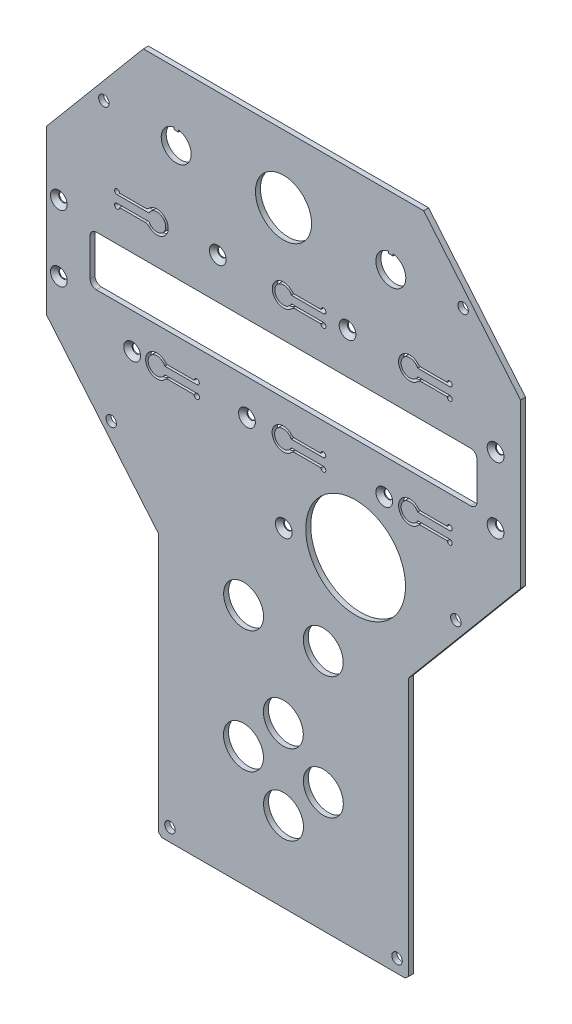
SolidWorks part; units mm, degrees
ref_plane "Plano frontal" through (0, 0, 0) normal (0, 0, 1) x (1, 0, 0)
ref_plane "Plano superior" through (0, 0, 0) normal (0, 1, 0) x (1, 0, 0)
ref_plane "Plano direito" through (0, 0, 0) normal (1, 0, 0) x (0, 0, -1)
sketch "Esboço1" plane through (0, 0, 0) normal (0, 0, 1) x (1, 0, 0)
  line L6 (55.321, 133.8096) -> (-57.007, 133.8096)
  line L7 (-57.007, 133.8096) -> (-95.843, 87.5267)
  line L8 (-95.843, 87.5267) -> (-95.843, 22.1402)
  line L9 (-95.843, 22.1402) -> (-50.843, -31.4887)
  line L10 (-50.843, -31.4887) -> (-50.843, -135.0827)
  line L11 (-50.843, -135.0827) -> (-49.5229, -136.1904)
  line L12 (-49.5229, -136.1904) -> (47.8369, -136.1904)
  line L13 (49.157, -135.0827) -> (47.8369, -136.1904)
  line L14 (49.157, -31.4887) -> (49.157, -135.0827)
  line L15 (94.157, 22.1402) -> (49.157, -31.4887)
  line L16 (94.157, 87.5267) -> (94.157, 22.1402)
  line L17 (55.321, 133.8096) -> (94.157, 87.5267)
  point P16 (-0.843, -136.1904)
  point P17 (-0.843, 133.8096)
extrude "Ressalto-extrusão1" add sketch "Esboço1" along normal blind 2
sketch "Esboço2" plane through (0, 0, 2) normal (0, 0, 1) x (1, 0, 0)
  line L0 (-0.843, -146.6722) -> (-0.843, 180.0647) construction
  line L1 (-95.843, 87.5267) -> (-95.843, 22.1402) construction
  line L2 (55.321, 133.8096) -> (-57.007, 133.8096) construction
  line L3 (-95.843, 22.1402) -> (-50.843, -31.4887) construction
  line L6 (49.157, -135.0827) -> (49.157, -31.4887) construction
  line L7 (-49.5229, -136.1904) -> (47.8369, -136.1904) construction
  line L9 (-50.843, -31.4887) -> (-50.843, -135.0827) construction
  circle A0 centre (-72.8144, 107.9499) radius 2.1
  circle A1 centre (-46.343, -130.9644) radius 2.1
  circle A2 centre (44.657, -130.9644) radius 2.1
  circle A3 centre (71.1284, 107.9499) radius 2.1
  circle A4 centre (-69.8958, -1.7817) radius 2.1
  circle A5 centre (68.2098, -1.7817) radius 2.1
  dimension "D1" = 23.0286
  dimension "D2" = 4.5
  dimension "D3" = 4.5
  dimension "D7" = 25.8597
  dimension "D4" = 5.226
  dimension "D11" = 4.5
extrude "Corte-extrusão1" cut sketch "Esboço2" against normal up to next
sketch "Esboço3" plane through (0, 0, 2) normal (0, 0, 1) x (1, 0, 0)
  line L0 (-95.843, 87.5267) -> (-95.843, 22.1402) construction
  line L1 (-49.5229, -136.1904) -> (47.8369, -136.1904) construction
  line L2 (-75.843, 40.8096) -> (74.157, 40.8096)
  line L3 (-78.343, 43.3096) -> (-78.343, 58.3096)
  line L4 (-75.843, 60.8096) -> (74.157, 60.8096)
  line L5 (76.657, 43.3096) -> (76.657, 58.3096)
  line L6 (-78.343, 40.8096) -> (76.657, 60.8096) construction
  line L7 (-78.343, 60.8096) -> (76.657, 40.8096) construction
  arc A0 (74.157, 60.8096) -> (76.657, 58.3096) centre (74.157, 58.3096) cw
  arc A1 (74.157, 40.8096) -> (76.657, 43.3096) centre (74.157, 43.3096) ccw
  arc A2 (-75.843, 40.8096) -> (-78.343, 43.3096) centre (-75.843, 43.3096) cw
  arc A3 (-78.343, 58.3096) -> (-75.843, 60.8096) centre (-75.843, 58.3096) cw
  dimension "D1" = 2.5
  dimension "D2" = 155
  dimension "D3" = 20
  dimension "D4" = 17.5
  dimension "D5" = 177
extrude "Corte-extrusão2" cut sketch "Esboço3" against normal up to next
sketch "Esboço4" plane through (0, 0, 2) normal (0, 0, 1) x (1, 0, 0)
  line L2 (-49.5229, -136.1904) -> (47.8369, -136.1904) construction
  line L3 (94.157, 22.1402) -> (94.157, 87.5267) construction
  circle A0 centre (28.0563, -0.1904) radius 20
  dimension "D1" = 136
  dimension "D2" = 66.1007
extrude "Corte-extrusão3" cut sketch "Esboço4" against normal up to next
sketch "Esboço5" plane through (0, 0, 2) normal (0, 0, 1) x (1, 0, 0)
  line L2 (55.321, 133.8096) -> (-57.007, 133.8096) construction
  line L3 (-44.743, 112.7417) -> (-44.743, 111.9417)
  line L4 (-44.743, 111.9417) -> (-42.943, 111.9417)
  line L5 (-42.943, 111.9417) -> (-42.943, 112.7417)
  line L6 (41.257, 112.7417) -> (41.257, 111.9417)
  line L7 (41.257, 111.9417) -> (43.057, 111.9417)
  line L8 (43.057, 111.9417) -> (43.057, 112.7417)
  circle A0 centre (-16.8949, -88.1059) radius 8
  circle A1 centre (15.1229, -88.1059) radius 8
  circle A2 centre (-0.843, -104.1412) radius 8
  circle A3 centre (-0.9097, -72.1234) radius 8
  circle A4 centre (-16.8357, -39.1393) radius 8
  circle A5 centre (15.0819, -39.1108) radius 8
  circle A6 centre (-0.843, 106.8096) radius 11.25
  arc A7 (-44.743, 112.7417) -> (-42.943, 112.7417) centre (-43.843, 106.8096) ccw
  arc A8 (41.257, 112.7417) -> (43.057, 112.7417) centre (42.157, 106.8096) ccw
  dimension "D11" = 27
  dimension "D12" = 43
  dimension "D13" = 43
  dimension "D14" = 22.5
  dimension "D15" = 12
  dimension "D16" = 12
  dimension "D18" = 1.8
  dimension "D19" = 0.9
  dimension "D20" = 0.8
  dimension "D21" = 1.8
  dimension "D22" = 0.9
  dimension "D23" = 0.8
extrude "Corte-extrusão4" cut sketch "Esboço5" against normal up to next
sketch "Esboço10" plane through (0, 0, 2) normal (0, 0, 1) x (1, 0, 0)
  line L3 (94.157, 22.1402) -> (94.157, 87.5267) construction
  line L4 (74.157, 60.8096) -> (-75.843, 60.8096) construction
  circle A0 centre (-61.4827, 26.6206) radius 1.75
  circle A1 centre (-15.4827, 26.6206) radius 1.75
  circle A2 centre (39.5173, 26.6206) radius 1.75
  circle A3 centre (84.131, 37.971) radius 1.6
  circle A4 centre (84.131, 64.471) radius 1.6
  circle A5 centre (-90.869, 64.471) radius 1.6
  circle A6 centre (-90.869, 37.971) radius 1.6
  circle A7 centre (-27.183, 77.1996) radius 1.75
  circle A8 centre (24.817, 77.1996) radius 1.75
  circle A9 centre (-0.7327, -4.3294) radius 2
  dimension "D1" = 69.3401
  dimension "D2" = 16.39
  dimension "D3" = 52
  dimension "D4" = 30.95
  dimension "D5" = 14.75
hole_wizard "Escareado para parafuso Allen sextavado escareado de M32" positions "3DSketch3" profile "Esboço11" countersink size "M3" standard "ISO" end condition through all
sketch3d "3DSketch3"
  point P0 (-90.869, 64.471, 2)
  point P3 (-90.869, 37.971, 2)
  point P6 (-61.4827, 26.6206, 2)
  point P9 (-15.4827, 26.6206, 2)
  point P12 (39.5173, 26.6206, 2)
  point P15 (84.131, 37.971, 2)
  point P18 (84.131, 64.471, 2)
  point P21 (24.817, 77.1996, 2)
  point P24 (-27.183, 77.1996, 2)
  point P32 (-0.7327, -4.3294, 2)
sketch "Esboço11" plane through (-90.869, 64.471, 2) normal (1, 0, 0) x (0, -1, 0)
  line L0 (0, 0) -> (0, 2)
  line L1 (0, 2) -> (1.7, 2)
  line L2 (1.7, 2) -> (1.7, 1.66)
  line L3 (1.7, 1.66) -> (3.36, 0)
  line L5 (3.36, 0) -> (0, 0)
  line L6 (-1.7, 1.66) -> (-3.36, 0) construction
  line L11 (0, -6.35) -> (0, 107.95) construction
  dimension "Thru Hole Dia." = 3.4
  dimension "Thru Hole Depth" = 2
  dimension "Near C'Sink Dia." = 6.72
  dimension "Near C'Sink Angle" = 90
sketch "Esboço12" plane through (0, 0, 2) normal (0, 0, 1) x (1, 0, 0)
  line L0 (-75.843, 40.8096) -> (74.157, 40.8096) construction
  line L1 (74.157, 60.8096) -> (-75.843, 60.8096) construction
  line L2 (94.157, 22.1402) -> (94.157, 87.5267) construction
  line L3 (52.9293, 28.0196) -> (65.767, 28.0196)
  line L5 (64.767, 29.0196) -> (53.5087, 29.0196)
  line L6 (52.9293, 25.0196) -> (65.767, 25.0196)
  line L7 (2.2593, 28.0196) -> (15.097, 28.0196)
  line L8 (64.767, 24.0196) -> (53.5087, 24.0196)
  line L9 (14.097, 24.0196) -> (2.8387, 24.0196)
  line L10 (14.097, 29.0196) -> (2.8387, 29.0196)
  line L11 (2.2593, 25.0196) -> (15.097, 25.0196)
  line L12 (-48.4107, 28.0196) -> (-35.573, 28.0196)
  line L13 (-36.6534, 24.0196) -> (-47.8313, 24.0196)
  line L14 (-36.573, 29.0196) -> (-47.8313, 29.0196)
  line L15 (-48.4107, 25.0196) -> (-35.9821, 25.0196)
  line L25 (2.3293, 77.9796) -> (15.167, 77.9796)
  line L26 (52.9293, 77.9796) -> (65.767, 77.9796)
  line L27 (14.167, 78.9796) -> (2.9087, 78.9796)
  line L28 (2.3293, 74.9796) -> (15.167, 74.9796)
  line L29 (-54.6953, 77.9796) -> (-67.533, 77.9796)
  line L30 (14.167, 73.9796) -> (2.9087, 73.9796)
  line L31 (64.767, 78.9796) -> (53.5087, 78.9796)
  line L32 (52.9293, 74.9796) -> (65.767, 74.9796)
  line L34 (64.767, 73.9796) -> (53.5087, 73.9796)
  line L35 (-66.533, 78.9796) -> (-55.2746, 78.9796)
  line L36 (-54.6953, 74.9796) -> (-67.533, 74.9796)
  line L38 (-66.533, 73.9796) -> (-55.2746, 73.9796)
  arc A0 (53.5087, 29.0196) -> (53.5087, 24.0196) centre (49.767, 26.5196) ccw
  arc A2 (15.097, 25.0196) -> (14.097, 24.0196) centre (15.097, 24.0196) cw
  arc A3 (-47.8313, 29.0196) -> (-47.8313, 24.0196) centre (-51.573, 26.5196) ccw
  arc A4 (-55.2746, 73.9796) -> (-55.2746, 78.9796) centre (-51.533, 76.4796) ccw
  arc A5 (2.9087, 78.9796) -> (2.9087, 73.9796) centre (-0.833, 76.4796) ccw
  arc A6 (53.5087, 78.9796) -> (53.5087, 73.9796) centre (49.767, 76.4796) ccw
  arc A7 (52.9293, 28.0196) -> (52.9293, 25.0196) centre (49.767, 26.5196) ccw
  arc A8 (65.767, 28.0196) -> (64.767, 29.0196) centre (65.767, 29.0196) ccw
  arc A9 (64.767, 24.0196) -> (65.767, 25.0196) centre (65.767, 24.0196) ccw
  arc A10 (15.097, 28.0196) -> (14.097, 29.0196) centre (15.097, 29.0196) ccw
  arc A11 (2.8387, 29.0196) -> (2.8387, 24.0196) centre (-0.903, 26.5196) ccw
  arc A12 (2.2593, 28.0196) -> (2.2593, 25.0196) centre (-0.903, 26.5196) ccw
  arc A13 (-35.573, 28.0196) -> (-36.573, 29.0196) centre (-35.573, 29.0196) ccw
  arc A14 (-35.9821, 25.0196) -> (-36.6534, 24.0196) centre (-35.573, 24.0196) cw
  arc A17 (-48.4107, 28.0196) -> (-48.4107, 25.0196) centre (-51.573, 26.5196) ccw
  arc A22 (15.167, 77.9796) -> (14.167, 78.9796) centre (15.167, 78.9796) ccw
  arc A23 (52.9293, 77.9796) -> (52.9293, 74.9796) centre (49.767, 76.4796) ccw
  arc A24 (2.3293, 77.9796) -> (2.3293, 74.9796) centre (-0.833, 76.4796) ccw
  arc A25 (14.167, 73.9796) -> (15.167, 74.9796) centre (15.167, 73.9796) ccw
  arc A26 (65.767, 77.9796) -> (64.767, 78.9796) centre (65.767, 78.9796) ccw
  arc A27 (64.767, 73.9796) -> (65.767, 74.9796) centre (65.767, 73.9796) ccw
  arc A28 (-54.6953, 74.9796) -> (-54.6953, 77.9796) centre (-51.533, 76.4796) ccw
  arc A29 (-66.533, 78.9796) -> (-67.533, 77.9796) centre (-67.533, 78.9796) ccw
  arc A30 (-67.533, 74.9796) -> (-66.533, 73.9796) centre (-67.533, 73.9796) ccw
  dimension "D2" = 14.29
  dimension "D5" = 15.67
  dimension "D6" = 44.39
  dimension "D7" = 50.6
  dimension "D8" = 50.7
  dimension "D9" = 1
  dimension "D13" = 16
  dimension "D14" = 4.5
  dimension "D15" = 3.5
  dimension "D16" = 3.5
  dimension "D17" = 4.5
  dimension "D10" = 1
  dimension "D18" = 16
  dimension "D22" = 3.5
  dimension "D19" = 44.39
  dimension "D33" = 4.5
  dimension "D38" = 4.5
  dimension "D42" = 1
  dimension "D39" = 3.5
  dimension "D44" = 16
  dimension "D46" = 4.5
  dimension "D47" = 3.5
  dimension "D45" = 16
  dimension "D50" = 4.5
  dimension "D51" = 3.5
  dimension "D52" = 16
  dimension "D21" = 50.67
  dimension "D11" = 3
  dimension "D12" = 1.5
  dimension "D20" = 50.67
  dimension "D23" = 16
  dimension "D40" = 3
  dimension "D41" = 1.5
  dimension "D43" = 1
extrude "Corte-extrusão5" cut sketch "Esboço12" against normal blind 10
fillet "Filete1" radius 2 11 edges at (-47.8313, 24.0196, 1) (2.8387, 24.0196, 1) (53.5087, 73.9796, 1) (-47.8313, 29.0196, 1) (2.8387, 29.0196, 1) (53.5087, 29.0196, 1) (53.5087, 78.9796, 1) (2.9087, 73.9796, 1) (2.9087, 78.9796, 1) (-55.2746, 73.9796, 1) (-55.2746, 78.9796, 1)
